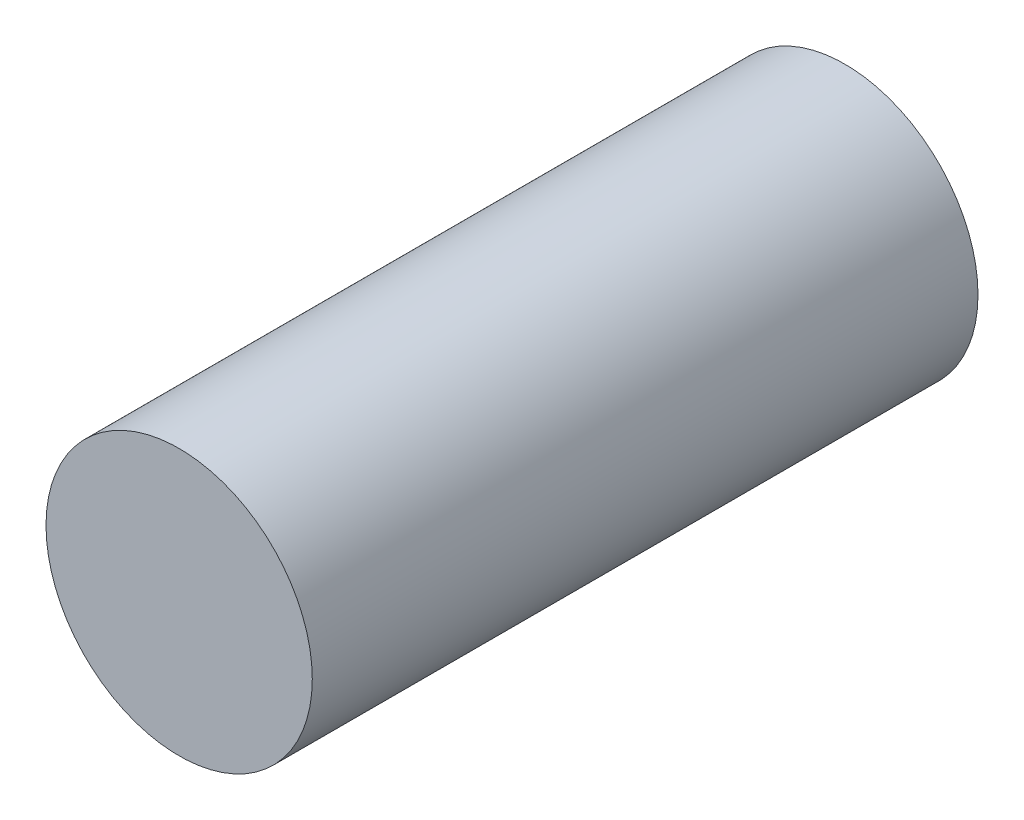
SolidWorks part; units mm, degrees
material "1060 Alloy"
ref_plane "Front Plane" through (0, 0, 0) normal (0, 0, 1) x (1, 0, 0)
ref_plane "Top Plane" through (0, 0, 0) normal (0, 1, 0) x (1, 0, 0)
ref_plane "Right Plane" through (0, 0, 0) normal (1, 0, 0) x (0, 0, -1)
sketch "Sketch1" plane through (0, 0, 0) normal (0, 0, 1) x (1, 0, 0)
  circle A0 centre (0, 0) radius 2
  dimension "D1" = 4
extrude "Boss-Extrude1" add sketch "Sketch1" along normal blind 10
